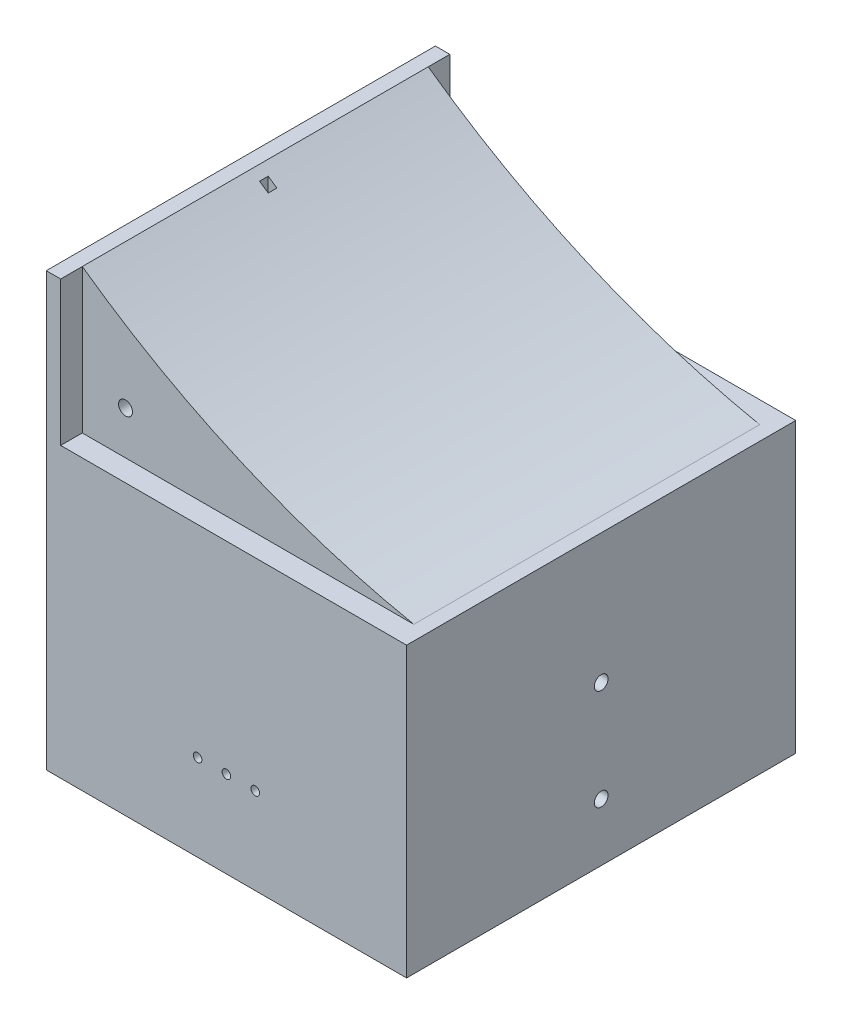
SolidWorks part; units mm, degrees
material "ABS"
ref_plane "Front" through (0, 0, 0) normal (0, 0, 1) x (1, 0, 0)
ref_plane "Top" through (0, 0, 0) normal (0, 1, 0) x (1, 0, 0)
ref_plane "Right" through (0, 0, 0) normal (1, 0, 0) x (0, 0, -1)
sketch "Sketch3" plane through (0, 0, 0) normal (0, 0, 1) x (1, 0, 0)
  line L0 (0, 0) -> (120, 0)
  line L1 (120, 0) -> (120, 100)
  line L2 (0, 0) -> (0, 150)
  line L3 (120, 100) -> (115, 100)
  arc A1 (0, 150) -> (115, 100) centre (174.4762, 394.0452) ccw
  dimension "D4" = 300
  dimension "D1" = 100
  dimension "D2" = 120
  dimension "D3" = 150
  dimension "D5" = 5
extrude "Boss-Extrude2" add sketch "Sketch3" along normal mid plane 120
sketch "Sketch4" plane through (0, 0, 60) normal (0, 0, 1) x (1, 0, 0)
  line L1 (0, 0) -> (120, 0)
  line L2 (0, 0) -> (0, 100)
  line L3 (0, 100) -> (120, 100)
  line L4 (120, 0) -> (120, 100)
extrude "Boss-Extrude3" add sketch "Sketch4" along normal blind 7.5
mirror "Mirror1" about plane through (0, 0, 0) normal (0, 0, 1) of "Boss-Extrude3"
sketch "Sketch5" plane through (0, 0, 0) normal (-1, 0, 0) x (0, 0, 1)
  line L0 (60, 150) -> (-60, 150) construction
  line L1 (-67.5, 0) -> (67.5, 0)
  line L2 (-67.5, 0) -> (-67.5, 150)
  line L3 (-67.5, 150) -> (67.5, 150)
  line L4 (67.5, 0) -> (67.5, 150)
extrude "Boss-Extrude4" add sketch "Sketch5" along normal blind 5
sketch "Sketch6" plane through (0, 0, 0) normal (0, -1, 0) x (1, 0, 0)
  line L0 (120, 67.5) -> (120, -67.5) construction
  line L6 (-5, -67.5) -> (-5, 67.5) construction
  line L7 (-5, 37.5) -> (107.3, 37.5)
  line L8 (-5, 37.5) -> (-5, -37.5)
  line L9 (-5, -37.5) -> (107.3, -37.5)
  line L10 (107.3, 37.5) -> (107.3, -37.5)
  point P6 (-5, 0)
  dimension "D1" = 12.7
  dimension "D2" = 75
extrude "Cut-Extrude2" cut sketch "Sketch6" against normal blind 75
sketch "Sketch7" plane through (107.3, 0, 0) normal (-1, 0, 0) x (0, 0, 1)
  line L0 (0, 0) -> (0, 75) construction
  line L1 (-37.5, 0) -> (37.5, 0) construction
  line L2 (-37.5, 75) -> (37.5, 75) construction
  line L3 (37.5, 75) -> (-37.5, 75) construction
  point P6 (0, 55)
  point P7 (0, 20)
  dimension "D1" = 20
  dimension "D2" = 20
hole_wizard "#10 Clearance Hole1" positions "Sketch8" profile "Sketch9" hole size "#10" standard "ANSI Inch" end condition through all
sketch "Sketch8" plane through (107.3, 0, 0) normal (-1, 0, 0) x (0, 0, 1)
  point P0 (0, 55)
  point P3 (0, 20)
sketch "Sketch9" plane through (107.3, 55, 0) normal (0, 1, 0) x (0, 0, 1)
  line L0 (0, 0) -> (0, 12.7)
  line L1 (0, 12.7) -> (2.3876, 12.7)
  line L2 (2.3876, 12.7) -> (2.3876, 0)
  line L5 (2.3876, 0) -> (0, 0)
  line L11 (0, -6.35) -> (0, 107.95) construction
  dimension "Thru Hole Dia." = 4.7752
  dimension "Thru Hole Depth" = 12.7
sketch "Sketch10" plane through (0, 75, 0) normal (0, -1, 0) x (1, 0, 0)
  line L0 (20, 29.5) -> (20, -18.5) construction
  line L1 (-5, 37.5) -> (-5, -37.5) construction
  line L4 (107.3, 37.5) -> (-5, 37.5) construction
  line L5 (72, 14.25) -> (72, -13.75) construction
  dimension "D1" = 48
  dimension "D2" = 25
  dimension "D3" = 8
  dimension "D4" = 28
  dimension "D5" = 4.75
  dimension "D6" = 52
hole_wizard "#2 Clearance Hole1" positions "Sketch11" profile "Sketch12" hole size "#2" standard "ANSI Inch"
sketch "Sketch11" plane through (0, 75, 0) normal (0, -1, 0) x (-1, 0, 0)
  point P3 (-20, 18.5)
  point P6 (-72, -14.25)
  point P9 (-72, 13.75)
  point P13 (-21.143, -29.5)
  dimension "D1" = 1.143
sketch "Sketch12" plane through (20, 75, -18.5) normal (1, 0, 0) x (0, 0, -1)
  line L0 (0, 0) -> (0, 6.9605)
  line L1 (0, 6.9605) -> (1.016, 6.35)
  line L2 (1.016, 6.35) -> (1.016, 0)
  line L5 (1.016, 0) -> (0, 0)
  line L10 (0, 6.9605) -> (-1.016, 6.35) construction
  line L11 (0, -6.35) -> (0, 107.95) construction
  dimension "Hole Dia." = 2.032
  dimension "Hole Depth" = 6.35
  dimension "Drill Angle" = 118
hole_wizard "#10 Clearance Hole2" positions "Sketch14" profile "Sketch15" hole size "#10" standard "ANSI Inch"
sketch "Sketch14" plane through (0, 0, 60) normal (0, 0, 1) x (1, 0, 0)
  line L0 (120, 100) -> (0, 100) construction
  line L1 (0, 100) -> (0, 150) construction
  point P0 (15, 115)
  dimension "D1" = 15
  dimension "D2" = 15
sketch "Sketch15" plane through (15, 115, 60) normal (1, 0, 0) x (0, -1, 0)
  line L0 (0, 0) -> (0, 26.8499)
  line L1 (0, 26.8499) -> (2.413, 25.4)
  line L2 (2.413, 25.4) -> (2.413, 0)
  line L5 (2.413, 0) -> (0, 0)
  line L10 (0, 26.8499) -> (-2.413, 25.4) construction
  line L11 (0, -6.35) -> (0, 107.95) construction
  dimension "Hole Dia." = 4.826
  dimension "Hole Depth" = 25.4
  dimension "Drill Angle" = 118
mirror "Mirror2" about plane through (0, 0, 0) normal (0, 0, 1) of "#10 Clearance Hole2"
sketch "Sketch17" plane through (0, 75, 0) normal (0, -1, 0) x (1, 0, 0)
  line L5 (3, 0) -> (-5, 0) construction
  line L6 (3, -1.5) -> (6, -1.5)
  line L7 (3, -1.5) -> (3, 1.5)
  line L8 (3, 1.5) -> (6, 1.5)
  line L9 (6, -1.5) -> (6, 1.5)
  line L10 (-5, 37.5) -> (-5, -37.5) construction
  dimension "D1" = 3
  dimension "D2" = 8
extrude "Cut-Extrude4" cut sketch "Sketch17" against normal through all
sketch "Sketch18" plane through (0, 0, 37.5) normal (0, 0, -1) x (-1, 0, 0)
  line L0 (-120, 30) -> (5, 30) construction
  line L1 (5, 75) -> (5, 0) construction
  line L2 (-120, 0) -> (-120, 100) construction
  line L3 (-107.3, 0) -> (5, 0) construction
  circle A0 centre (-67.5, 30) radius 2.5
  circle A1 centre (-57.5, 30) radius 2.5
  circle A2 centre (-47.5, 30) radius 2.5
  dimension "D3" = 5
  dimension "D1" = 10
  dimension "D2" = 10
  dimension "D4" = 30
extrude "Cut-Extrude5" cut sketch "Sketch18" against normal offset from surface (27 mm away) 3 up to face at (38.3333, 83.3333, 67.5)
sketch "Sketch19" plane through (0, 0, 64.5) normal (0, 0, -1) x (-1, 0, 0)
  circle A0 centre (-67.5, 30) radius 1.5
  circle A1 centre (-57.5, 30) radius 1.5
  circle A2 centre (-47.5, 30) radius 1.5
  dimension "D1" = 3
extrude "Cut-Extrude6" cut sketch "Sketch19" against normal through all
